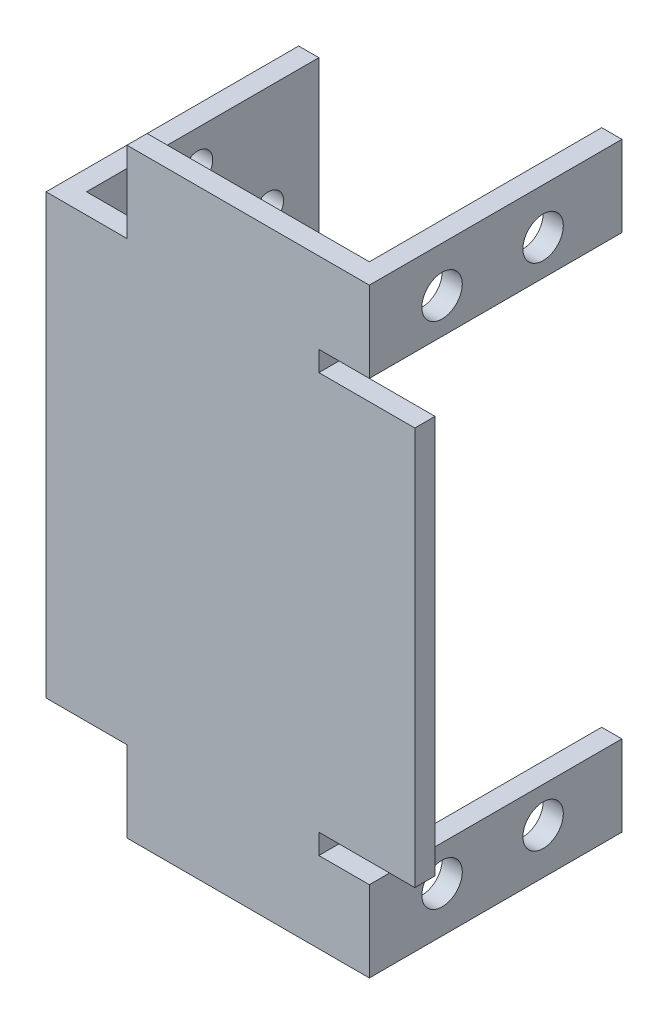
SolidWorks part; units mm, degrees
ref_plane "Plan de face" through (0, 0, 0) normal (0, 0, 1) x (1, 0, 0)
ref_plane "Plan de dessus" through (0, 0, 0) normal (0, 1, 0) x (1, 0, 0)
ref_plane "Plan de droite" through (0, 0, 0) normal (1, 0, 0) x (0, 0, -1)
sketch "Esquisse1" plane through (0, 0, 0) normal (0, 0, 1) x (1, 0, 0)
  line L0 (8.75, 17) -> (8.75, 19)
  line L4 (18.25, -22.4) -> (18.25, 17)
  line L5 (8.75, 19) -> (-10.25, 19) construction
  line L6 (-10.25, 19) -> (-18.25, 19)
  line L7 (8.75, 19) -> (13.75, 19)
  line L8 (13.75, 19) -> (13.75, 27)
  line L9 (13.75, 27) -> (-10.25, 27)
  line L10 (-10.25, 27) -> (-10.25, 19)
  line L11 (-18.25, -2.7) -> (18.25, -2.7) construction
  line L17 (8.75, 17) -> (18.25, 17)
  line L20 (-18.25, 19) -> (-18.25, -24.4)
  line L21 (8.75, -22.4) -> (18.25, -22.4)
  line L22 (-10.25, -32.4) -> (-10.25, -24.4)
  line L23 (13.75, -32.4) -> (-10.25, -32.4)
  line L24 (13.75, -24.4) -> (13.75, -32.4)
  line L25 (8.75, -24.4) -> (13.75, -24.4)
  line L26 (-10.25, -24.4) -> (-18.25, -24.4)
  line L27 (8.75, -22.4) -> (8.75, -24.4)
  point P0 (0, 0)
  point P18 (0, -5.4)
  dimension "D1" = 19.7
  dimension "D2" = 21.7
  dimension "D3" = 24
  dimension "D4" = 8
  dimension "D5" = 5
  dimension "D6" = 2
  dimension "D7" = 8
  dimension "D8" = 36.5
extrude "Boss.-Extru.1" add sketch "Esquisse1" along normal blind 2
sketch "Esquisse2" plane through (0, 0, 0) normal (0, 0, -1) x (-1, 0, 0)
  line L0 (16.25, 19) -> (18.25, 19)
  line L2 (18.25, 19) -> (18.25, -24.4)
  line L3 (18.25, -24.4) -> (16.25, -24.4)
  line L5 (16.25, -24.4) -> (16.25, 19)
  line L9 (18.25, -24.4) -> (10.25, -24.4) construction
  dimension "D1" = 2
  dimension "D2" = 43.4
extrude "Boss.-Extru.2" add sketch "Esquisse2" along normal blind 23
sketch "Esquisse3" plane through (0, 27, 0) normal (0, 1, 0) x (1, 0, 0)
  line L0 (13.75, 0) -> (11.75, 0)
  line L1 (13.75, 0) -> (-10.25, 0) construction
  line L2 (11.75, 0) -> (11.75, 23)
  line L3 (11.75, 23) -> (13.75, 23)
  line L4 (13.75, 23) -> (13.75, 0)
  dimension "D1" = 2
  dimension "D2" = 23
extrude "Boss.-Extru.3" add sketch "Esquisse3" against normal blind 8
sketch "Esquisse8" plane through (0, -32.4, 0) normal (0, -1, 0) x (1, 0, 0)
  line L0 (13.75, 0) -> (11.75, 0)
  line L1 (11.75, 0) -> (11.75, -23)
  line L2 (11.75, -23) -> (13.75, -23)
  line L3 (13.75, -23) -> (13.75, 0)
  dimension "D1" = 2
extrude "Boss.-Extru.5" add sketch "Esquisse8" against normal blind 8
sketch "Esquisse9" plane through (13.75, 0, 0) normal (1, 0, 0) x (0, 0, -1)
  line L0 (-2, 19) -> (-2, 27) construction
  line L1 (-2, 19) -> (23, 19) construction
  line L2 (0, -2.7) -> (21.4042, -2.7) construction
  line L3 (0, -22.4) -> (0, 17) construction
  circle A0 centre (5.2, 22.5) radius 2
  circle A1 centre (15.2, 22.5) radius 2
  circle A2 centre (15.2, -27.9) radius 2
  circle A3 centre (5.2, -27.9) radius 2
  dimension "D1" = 4
  dimension "D2" = 4
  dimension "D3" = 10
  dimension "D4" = 3.5
  dimension "D5" = 3.5
  dimension "D6" = 7.2
extrude "Enlèv. mat.-Extru.3" cut sketch "Esquisse9" against normal blind 2
sketch "Esquisse10" plane through (-18.25, 0, 0) normal (-1, 0, 0) x (0, 0, 1)
  line L0 (-23, 19) -> (0, 19) construction
  line L1 (-23, -24.4) -> (-23, 19) construction
  line L2 (-23, -2.7) -> (2, -2.7) construction
  line L3 (2, 19) -> (2, -24.4) construction
  circle A0 centre (-11, 15.5) radius 1.5
  circle A1 centre (-11, 8.5) radius 1.5
  circle A2 centre (-4, 8.5) radius 1.5
  circle A3 centre (-11, 1.5) radius 1.5
  circle A4 centre (-18, 8.5) radius 1.5
  circle A5 centre (-11, -6.9) radius 1.5
  circle A6 centre (-11, -13.9) radius 1.5
  circle A7 centre (-4, -13.9) radius 1.5
  circle A8 centre (-18, -13.9) radius 1.5
  circle A9 centre (-11, -20.9) radius 1.5
  point P17 (-11, 8.5)
  dimension "D1" = 3
  dimension "D2" = 3
  dimension "D3" = 3.5
  dimension "D4" = 10.5
  dimension "D5" = 12
  dimension "D6" = 12
  dimension "D7" = 4
extrude "Enlèv. mat.-Extru.4" cut sketch "Esquisse10" against normal blind 2
